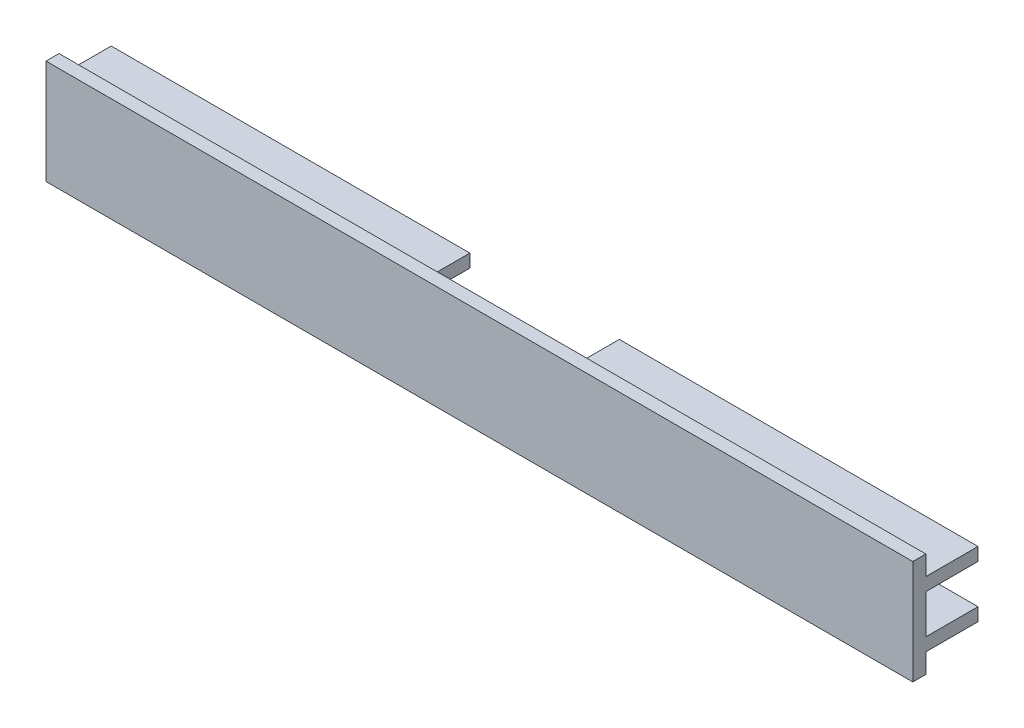
SolidWorks part; units mm, degrees
ref_plane "Front Plane" through (0, 0, 0) normal (0, 0, 1) x (1, 0, 0)
ref_plane "Top Plane" through (0, 0, 0) normal (0, 1, 0) x (1, 0, 0)
ref_plane "Right Plane" through (0, 0, 0) normal (1, 0, 0) x (0, 0, -1)
sketch "Sketch1" plane through (0, 0, 0) normal (1, 0, 0) x (0, 0, -1)
  line L0 (-3, 8) -> (-3, 5)
  line L1 (-5, 8) -> (-3, 8)
  line L2 (-5, 8) -> (-5, -8)
  line L3 (-5, -8) -> (-3, -8)
  line L4 (5, 5) -> (5, 3)
  line L5 (-5, 8) -> (5, -8) construction
  line L6 (-5, -8) -> (5, 8) construction
  line L7 (-3, 5) -> (5, 5)
  line L8 (5, 3) -> (-2, 3)
  line L9 (-2, 3) -> (-2, -3)
  line L10 (-2, -3) -> (5, -3)
  line L11 (5, -5) -> (-3, -5)
  line L12 (-3, -5) -> (-3, -8)
  line L13 (5, -3) -> (5, -5)
  point P0 (0, 0)
  dimension "D1" = 16
  dimension "D2" = 10
  dimension "D3" = 2
  dimension "D4" = 2
  dimension "D5" = 2
  dimension "D6" = 6
  dimension "D7" = 3
  dimension "D8" = 7
  dimension "D9" = 10
  dimension "D10" = 5
extrude "Extrude1" add sketch "Sketch1" along normal mid plane 132.92
sketch "Sketch2" plane through (-66.46, 0, 0) normal (-1, 0, 0) x (0, 0, 1)
  line L0 (2, 3) -> (3, 3)
  line L1 (3, 3) -> (3, -3)
  line L2 (3, -3) -> (2, -3)
  line L3 (2, -3) -> (2, 3)
  dimension "D1" = 1
extrude "Extrude2" cut sketch "Sketch2" against normal blind 32
sketch "Sketch3" plane through (66.46, 0, 0) normal (1, 0, 0) x (0, 0, -1)
  line L0 (-2, 3) -> (-3, 3)
  line L1 (-3, 3) -> (-3, -3)
  line L2 (-3, -3) -> (-2, -3)
  line L3 (-2, -3) -> (-2, 3) construction
  line L4 (-2, 3) -> (-2, -3)
  dimension "D1" = 1
extrude "Extrude3" cut sketch "Sketch3" against normal blind 32
sketch "Sketch4" plane through (0, 0, 2) normal (0, 0, -1) x (-1, 0, 0)
  line L0 (34.46, -3) -> (34.46, 3) construction
  line L1 (-34.46, -3) -> (-34.46, 3) construction
  line L2 (-34.46, 3) -> (-34.46, -3)
  line L3 (34.46, 3) -> (34.46, -3)
  arc A0 (34.46, 3) -> (34.46, -3) centre (34.46, 0) ccw
  arc A1 (-34.46, -3) -> (-34.46, 3) centre (-34.46, 0) ccw
extrude "Extrude4" cut sketch "Sketch4" against normal up to surface (1 mm away) up to face at (50.46, 0, 3)
sketch "Sketch5" plane through (0, 0, -5) normal (0, 0, -1) x (-1, 0, 0)
  line L0 (-66.46, 5) -> (66.46, 5) construction
  line L1 (-11.46, 5) -> (11.46, 5)
  line L2 (-11.46, 5) -> (-11.46, -5)
  line L3 (-11.46, -5) -> (11.46, -5)
  line L4 (11.46, 5) -> (11.46, -5)
  line L5 (-11.46, 5) -> (11.46, -5) construction
  line L6 (-11.46, -5) -> (11.46, 5) construction
  line L7 (-66.46, 3) -> (-66.46, 5) construction
  point P0 (0, 0)
  dimension "D1" = 55
extrude "Extrude5" cut sketch "Sketch5" against normal up to surface (7 mm away) up to face at (0, 0, 2)
